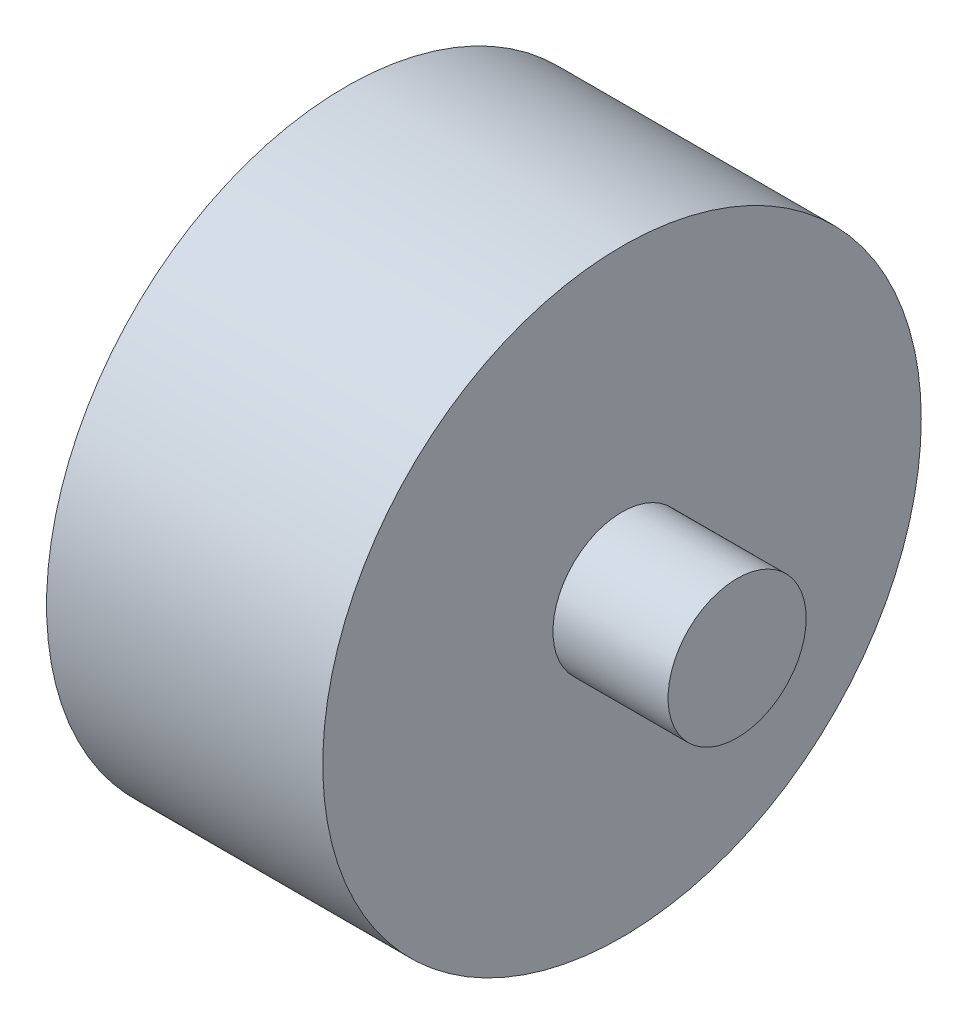
SolidWorks part; units mm, degrees
ref_plane "Front Plane" through (0, 0, 0) normal (0, 0, 1) x (1, 0, 0)
ref_plane "Top Plane" through (0, 0, 0) normal (0, 1, 0) x (1, 0, 0)
ref_plane "Right Plane" through (0, 0, 0) normal (1, 0, 0) x (0, 0, -1)
sketch "Sketch1" plane through (0, 0, 0) normal (1, 0, 0) x (0, 0, -1)
  circle A0 centre (0, 0) radius 65
  dimension "D1" = 130
extrude "Boss-Extrude1" add sketch "Sketch1" along normal blind 60
sketch "Sketch2" plane through (60, 0, 0) normal (1, 0, 0) x (0, 0, -1)
  circle A0 centre (0, 0) radius 15
  dimension "D1" = 30
extrude "Boss-Extrude2" add sketch "Sketch2" along normal blind 25
